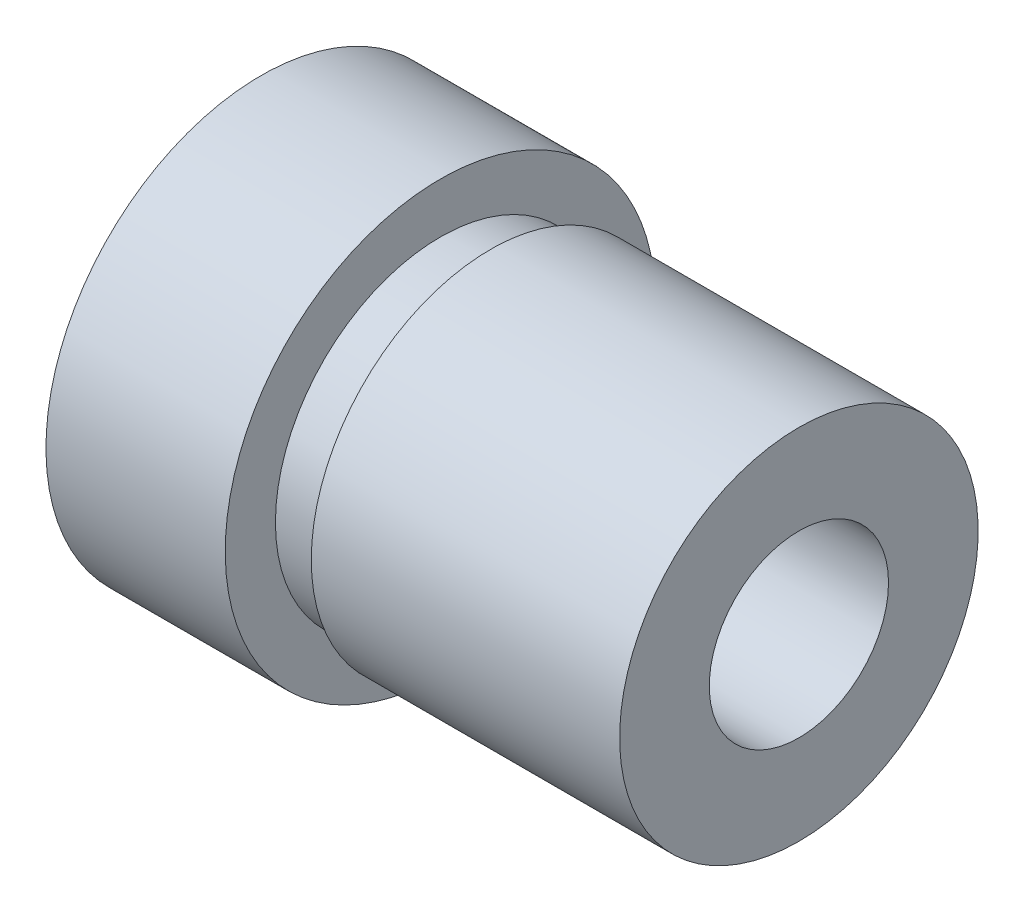
SolidWorks part; units mm, degrees
ref_plane "Front Plane" through (0, 0, 0) normal (0, 0, 1) x (1, 0, 0)
ref_plane "Top Plane" through (0, 0, 0) normal (0, 1, 0) x (1, 0, 0)
ref_plane "Right Plane" through (0, 0, 0) normal (1, 0, 0) x (0, 0, -1)
sketch "Sketch1" plane through (0, 0, 0) normal (0, 0, 1) x (1, 0, 0)
  line L0 (-3.75, 0) -> (-3.75, 3)
  line L1 (-3.75, 3) -> (-1.25, 3)
  line L2 (-1.25, 3) -> (-1.25, 2.5)
  line L3 (-1.25, 2.5) -> (3.75, 2.5)
  line L4 (3.75, 2.5) -> (3.75, 0)
  line L5 (3.75, 0) -> (-3.75, 0)
  line L7 (0, 0) -> (24.1532, 0) construction
  dimension "D1" = 5
  dimension "D2" = 6
  dimension "D3" = 2.5
  dimension "D4" = 5
revolve "Revolve1" add sketch "Sketch1" angle 360 about L7
hole_wizard "Trou taraudé M31" positions "Sketch3" profile "Sketch2" tap size "M3" standard "Iso" end condition through all
sketch "Sketch3" plane through (3.75, 0, 0) normal (1, 0, 0) x (0, 0, -1)
  point P0 (0, 0)
sketch "Sketch2" plane through (3.75, 0, 0) normal (0, 1, 0) x (0, 0, -1)
  line L0 (0, 0) -> (0, 7.5)
  line L1 (0, 7.5) -> (1.25, 7.5)
  line L2 (1.25, 7.5) -> (1.25, 0)
  line L5 (1.25, 0) -> (0, 0)
  line L11 (0, -6.35) -> (0, 107.95) construction
  dimension "Diamètre du trou pour taraudage jusqu'au prochain" = 2.5
  dimension "Profondeur du trou pour taraudage jusqu'au prochain" = 7.5
cosmetic thread "Filetage de perçage1" parameters "D2"=3
sketch "Sketch4" plane through (0, 0, 0) normal (0, 0, 1) x (1, 0, 0)
  line L0 (3.75, 2.5) -> (-1.25, 2.5) construction
  line L1 (-1.25, 3) -> (-0.55, 3)
  line L2 (-1.25, 3) -> (-1.25, 2.3)
  line L3 (-1.25, 2.3) -> (-0.55, 2.3)
  line L4 (-0.55, 3) -> (-0.55, 2.3)
  line L5 (-0.0903, 0) -> (5.195, 0) construction
  dimension "D1" = 0.2
  dimension "D2" = 0.7
revolve "Cut-Revolve1" cut sketch "Sketch4" angle 360 about L5
